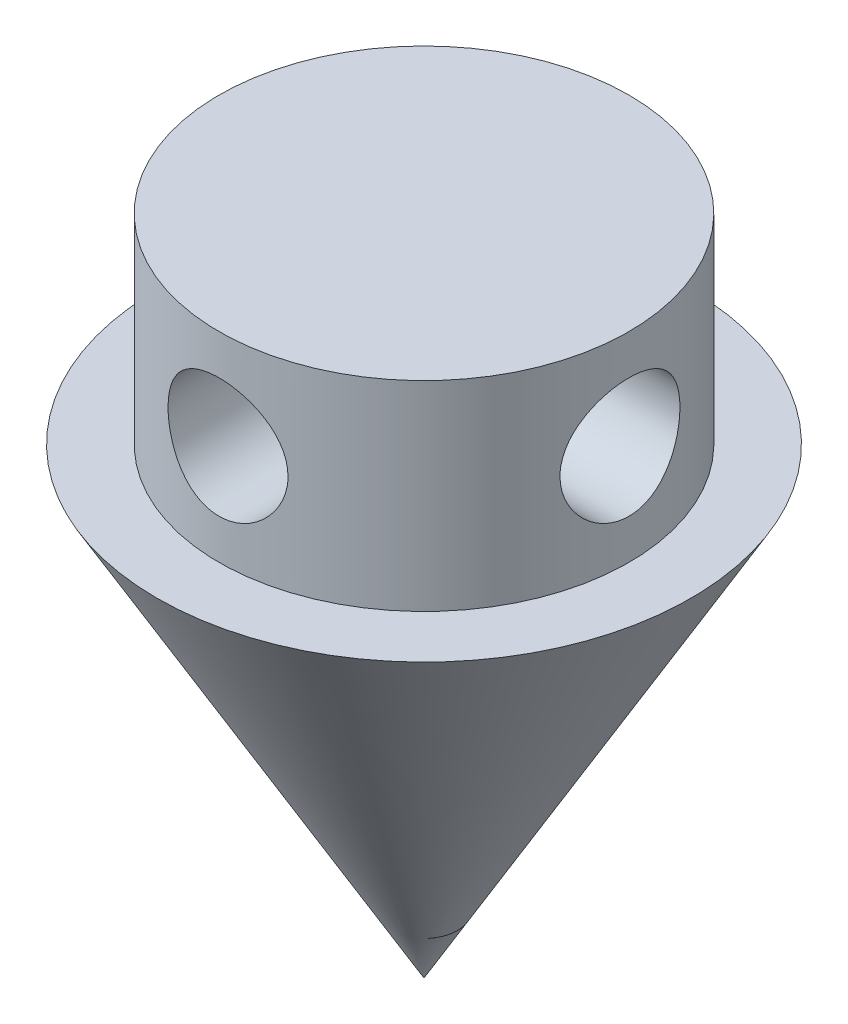
SolidWorks part; units mm, degrees
ref_plane "Front Plane" through (0, 0, 0) normal (0, 0, 1) x (1, 0, 0)
ref_plane "Top Plane" through (0, 0, 0) normal (0, 1, 0) x (1, 0, 0)
ref_plane "Right Plane" through (0, 0, 0) normal (1, 0, 0) x (0, 0, -1)
sketch "Sketch1" plane through (0, 0, 0) normal (0, 0, 1) x (1, 0, 0)
  line L0 (0, -16.5614) -> (0, 16.5614)
  line L1 (0, 16.5614) -> (10.25, 16.5614)
  line L2 (10.25, 16.5614) -> (10.25, 6.5614)
  line L3 (10.25, 6.5614) -> (13.35, 6.5614)
  line L4 (13.35, 6.5614) -> (0, -16.5614)
  line L5 (0, -24.5738) -> (0, 33.2277) construction
  dimension "D1" = 20.5
  dimension "D2" = 26.7
  dimension "D3" = 10
  dimension "D4" = 30
revolve "Revolve1" add sketch "Sketch1" angle 360 about L5
sketch "Sketch2" plane through (0, 0, 0) normal (0, 0, 1) x (1, 0, 0)
  line L0 (0, 16.5614) -> (0, 6.5614) construction
  line L1 (10.25, 16.5614) -> (-10.25, 16.5614) construction
  line L2 (13.35, 6.5614) -> (-13.35, 6.5614) construction
  circle A0 centre (0, 11.5614) radius 3
  dimension "D1" = 6
extrude "Cut-Extrude1" cut sketch "Sketch2" against normal through all both and the other way through all
pattern_circular "CirPattern1" count 2 over 90 about axis through (0, -24.5738, 0) along (0, -1, 0) of "Cut-Extrude1"
